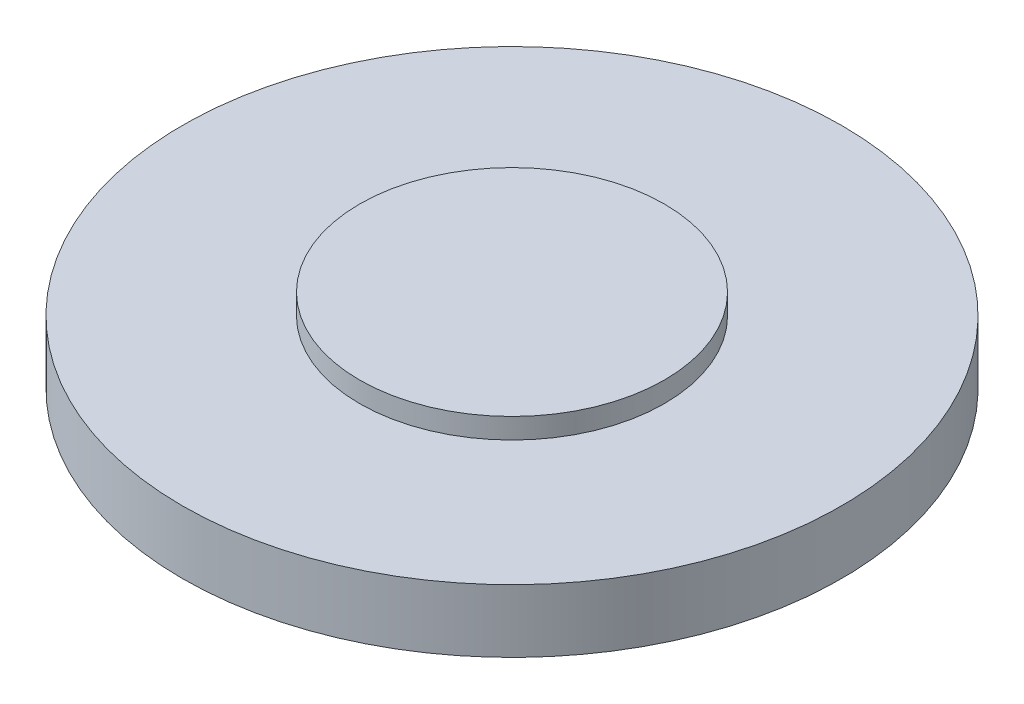
SolidWorks part; units mm, degrees
ref_plane "Front Plane" through (0, 0, 0) normal (0, 0, 1) x (1, 0, 0)
ref_plane "Top Plane" through (0, 0, 0) normal (0, 1, 0) x (1, 0, 0)
ref_plane "Right Plane" through (0, 0, 0) normal (1, 0, 0) x (0, 0, -1)
sketch "Sketch2" plane through (0, 0, 0) normal (0, 1, 0) x (1, 0, 0)
  circle A0 centre (0, 0) radius 19.35
  dimension "D1" = 38.7
extrude "Boss-Extrude1" add sketch "Sketch2" along normal blind 3.7
sketch "Sketch3" plane through (0, 3.7, 0) normal (0, 1, 0) x (1, 0, 0)
  circle A0 centre (0, 0) radius 8.95
  dimension "D1" = 17.9
extrude "Boss-Extrude2" add sketch "Sketch3" along normal blind 1.2
sketch "Sketch4" plane through (0, 0, 0) normal (0, -1, 0) x (1, 0, 0)
  circle A0 centre (0, 0) radius 18.55
  circle A1 centre (0, 0) radius 19.35 construction
  dimension "D1" = 0.8
extrude "Cut-Extrude1" cut sketch "Sketch4" against normal blind 1.5 contours A0
